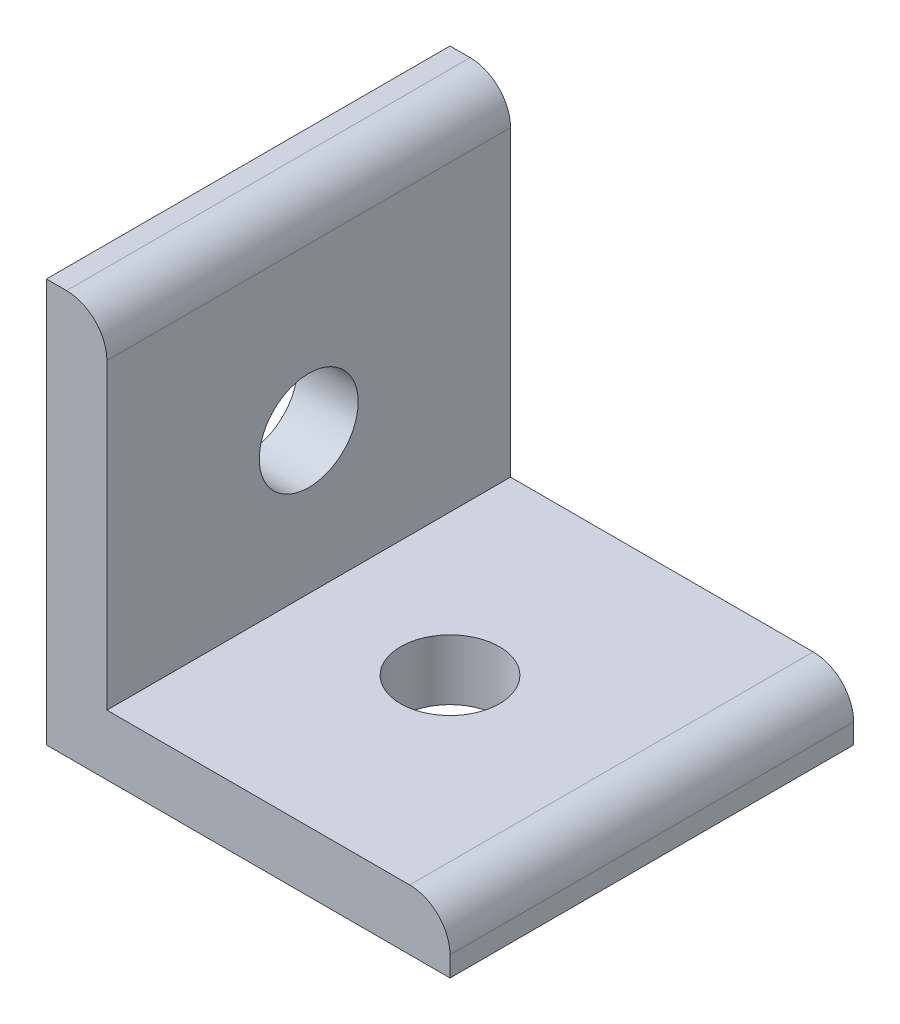
SolidWorks part; units mm, degrees
ref_plane "前视基准面" through (0, 0, 0) normal (0, 0, 1) x (1, 0, 0)
ref_plane "上视基准面" through (0, 0, 0) normal (0, 1, 0) x (1, 0, 0)
ref_plane "右视基准面" through (0, 0, 0) normal (1, 0, 0) x (0, 0, -1)
sketch "草图1" plane through (0, 0, 0) normal (0, 0, 1) x (1, 0, 0)
  line L0 (0, 0) -> (20.0016, 0)
  line L1 (0, 0) -> (0, 19.9969)
  line L2 (0, 19.9969) -> (2.9992, 19.9969)
  line L3 (2.9992, 19.9969) -> (2.9992, 2.9944)
  line L4 (2.9992, 2.9944) -> (20.0016, 2.9944)
  line L5 (20.0016, 2.9944) -> (20.0016, 0)
  dimension "D1" = 17.0024
  dimension "D2" = 17.0024
  dimension "D3" = 2.9992
  dimension "D4" = 2.9944
extrude "凸台-拉伸1" add sketch "草图1" along normal blind 20
sketch "草图3" plane through (2.9992, 0, 0) normal (1, 0, 0) x (0, 0, -1)
  line L0 (-20, 19.9969) -> (0, 19.9969) construction
  circle A0 centre (-10, 9.9969) radius 2.45
  dimension "D1" = 4.9
  dimension "D2" = 10
extrude "切除-拉伸1" cut sketch "草图3" against normal up to surface (2.9992 mm away) up to face at (0, 9.9984, 10)
sketch "草图5" plane through (0, 2.9944, 0) normal (0, 1, 0) x (1, 0, 0)
  line L0 (20.0016, -20) -> (20.0016, 0) construction
  circle A0 centre (10.0016, -10) radius 2.45
  dimension "D1" = 4.9
  dimension "D2" = 10
extrude "切除-拉伸2" cut sketch "草图5" against normal up to surface (2.9944 mm away) up to face at (10.0008, 0, 10)
fillet "圆角1" radius 2 1 edges at (2.9992, 19.9969, 10)
fillet "圆角2" radius 2 1 edges at (20.0016, 2.9944, 10)
ref_plane "Plane1" through (0, 0, 10) normal (0, 0, -1) x (-1, 0, 0)
sketch3d "3DSketch1"
  line L0 (0, 9.9969, 10) -> (2.9992, 9.9969, 10) construction
  line L1 (10.0016, 0, 10) -> (10.0016, 2.9944, 10) construction
  point P0 (0, 9.9969, 10)
  point P1 (10.0016, 0, 10)
